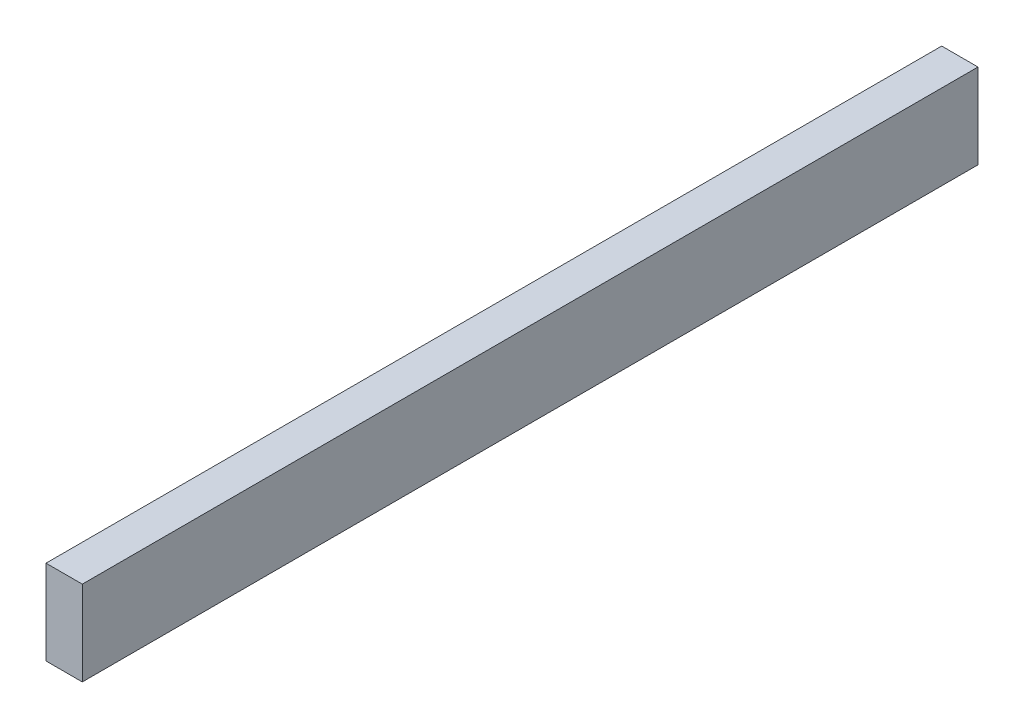
SolidWorks part; units mm, degrees
material "Pine"
ref_plane "Front Plane" through (0, 0, 0) normal (0, 0, 1) x (1, 0, 0)
ref_plane "Top Plane" through (0, 0, 0) normal (0, 1, 0) x (1, 0, 0)
ref_plane "Right Plane" through (0, 0, 0) normal (1, 0, 0) x (0, 0, -1)
sketch "Sketch1" plane through (0, 0, 0) normal (0, 0, 1) x (1, 0, 0)
  line L1 (-38.1, 64.4615) -> (0, 64.4615)
  line L2 (-38.1, 64.4615) -> (-38.1, -24.4385)
  line L3 (-38.1, -24.4385) -> (0, -24.4385)
  line L4 (0, 64.4615) -> (0, -24.4385)
  dimension "D1" = 88.9
  dimension "D2" = 38.1
extrude "Boss-Extrude1" add sketch "Sketch1" along normal blind 939.8
